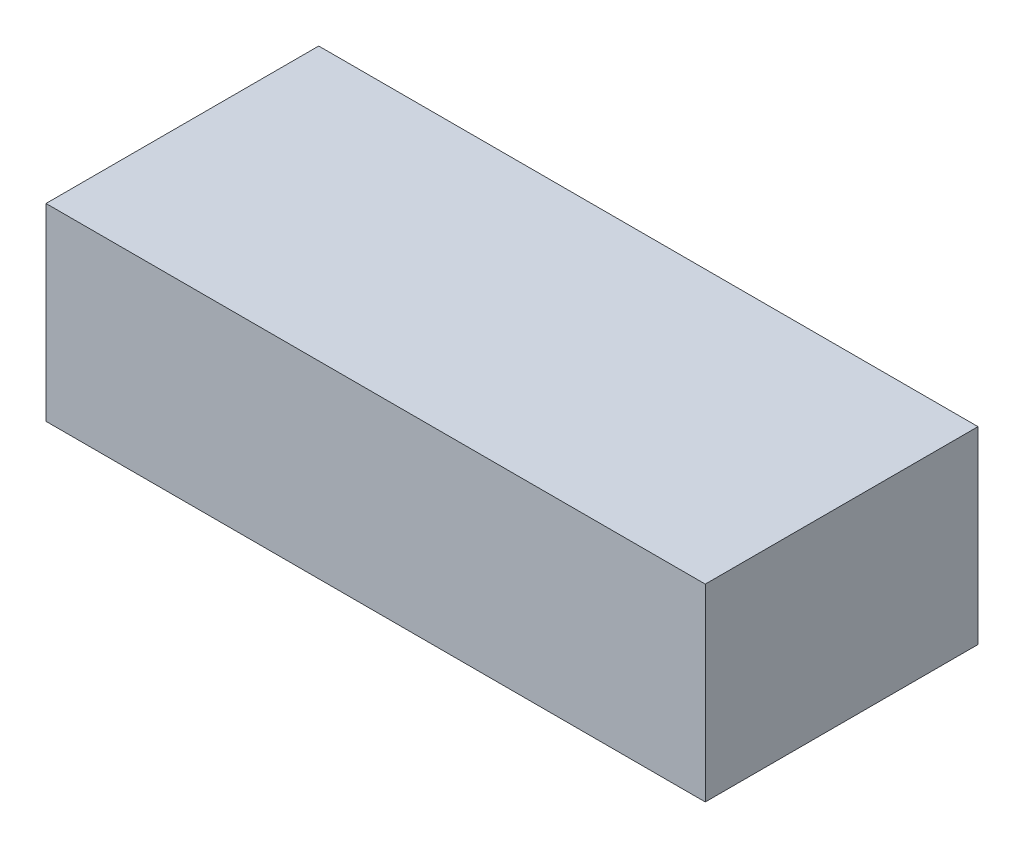
SolidWorks part; units mm, degrees
ref_plane "Alzado" through (0, 0, 0) normal (0, 0, 1) x (1, 0, 0)
ref_plane "Planta" through (0, 0, 0) normal (0, 1, 0) x (1, 0, 0)
ref_plane "Vista lateral" through (0, 0, 0) normal (1, 0, 0) x (0, 0, -1)
sketch "Croquis1" plane through (0, 0, 0) normal (0, 1, 0) x (1, 0, 0)
  line L1 (-35.052, -14.5) -> (35.052, -14.5)
  line L2 (-35.052, -14.5) -> (-35.052, 14.5)
  line L3 (-35.052, 14.5) -> (35.052, 14.5)
  line L4 (35.052, -14.5) -> (35.052, 14.5)
  line L5 (-35.052, -14.5) -> (35.052, 14.5) construction
  line L6 (-35.052, 14.5) -> (35.052, -14.5) construction
  point P0 (0, 0)
  dimension "D1" = 29
  dimension "D2" = 70.104
extrude "Saliente-Extruir1" add sketch "Croquis1" along normal blind 20.066
